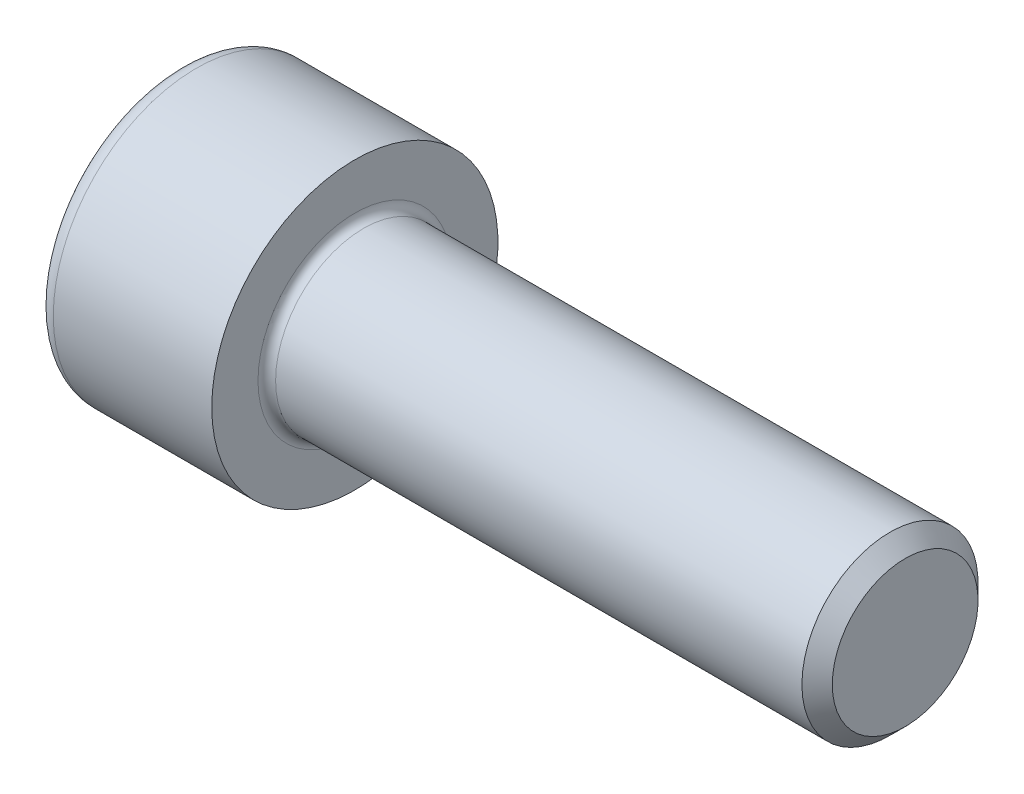
SolidWorks part; units mm, degrees
ref_plane "Plane1" through (0, 0, 0) normal (0, 0, 1) x (1, 0, 0)
ref_plane "Plane2" through (0, 0, 0) normal (0, 1, 0) x (1, 0, 0)
ref_plane "Plane3" through (0, 0, 0) normal (1, 0, 0) x (0, 0, -1)
sketch "BodySke" plane through (0, 0, 0) normal (0, 0, 1) x (1, 0, 0)
  line L0 (0, 0) -> (0, 6.5)
  line L1 (0, 6.5) -> (8, 6.5)
  line L2 (8, 6.5) -> (8, 4)
  line L3 (8, 4) -> (32.3095, 4)
  line L4 (33, 3.3095) -> (33, 0)
  line L5 (33, 0) -> (0, 0)
  line L6 (-31.75, 0) -> (127, 0) construction
  line L8 (33, 3.3095) -> (32.3095, 4)
  line L10 (33, -3.3095) -> (32.3095, -4) construction
  line L11 (9.25, 9.525) -> (9.25, 3.175) construction
  line L12 (8, 9.525) -> (8, 3.175) construction
  line L13 (-27, 9.525) -> (-27, 3.175) construction
  dimension "Diameter" = 8
  dimension "Head_ht" = 8
  dimension "Length" = 25
  dimension "Body_ch_ang" = 45
  dimension "Head_dia" = 13
  dimension "Minor_dia" = 6.619
  dimension "Advance" = 1.25
  dimension "Thread_nom" = 25
  dimension "Thread_length" = 60
revolve "Base-Revolve" add sketch "BodySke"
cosmetic thread "ThreadCosmetic" [suppressed]
fillet "Fillet1" radius 0.4 1 edges at (8, 0, 4)
fillet "Fillet2" radius 0.8 1 edges at (0, 0, 6.5)
sketch "Sketch2" plane through (0, 0, 0) normal (0, 0, 1) x (1, 0, 0)
  line L0 (0, 3.01) -> (4, 3.01)
  line L1 (4, 3.01) -> (5.7378, 0)
  line L2 (-31.75, 0) -> (127, 0) construction
  line L3 (5.7378, 0) -> (0, 0)
  line L4 (0, 0) -> (0, 3.01)
  line L6 (0, 0) -> (47.625, 0) construction
  dimension "D1" = 3.01
  dimension "D2" = 60
  dimension "Depth" = 4
revolve "Hex-PreBroach" cut sketch "Sketch2" angle 360 about L6
sketch "Sketch3" plane through (0, 0, 0) normal (-1, 0, 0) x (0, 0.5, 0.866)
  line L0 (1.7378, 3.01) -> (-1.7378, 3.01)
  line L1 (-1.7378, 3.01) -> (-3.4756, 0)
  line L2 (1.7378, 3.01) -> (3.4756, 0)
  line L3 (1.7378, -3.01) -> (3.4756, 0)
  line L4 (1.7378, -3.01) -> (-1.7378, -3.01)
  line L5 (-1.7378, -3.01) -> (-3.4756, 0)
  dimension "D1" = 3.01
  dimension "D2" = 3.01
  dimension "Hex_size" = 6.02
extrude "Hex" cut sketch "Sketch3" against normal blind 4
sketch "ThdSchSke" plane through (0, 0, 0) normal (0, 0, 1) x (1, 0, 0)
  line L0 (11.75, -3.3095) -> (11.2665, -4)
  line L1 (11.75, -3.3095) -> (12.2335, -4)
  line L2 (12.2335, -4) -> (12.2335, -5)
  line L3 (-3.175, 0) -> (5.1513, 0) construction
  line L4 (0, 5.7) -> (0, -5.7) construction
  line L5 (12.2335, -5) -> (11.2665, -5)
  line L6 (11.2665, -5) -> (11.2665, -4)
  dimension "Thread_minor" = 6.619
  dimension "Diameter" = 8
  dimension "Start" = 11.75
  dimension "SideAngle" = 55
  dimension "VeeAngle" = 70
  dimension "Overcut" = 10
revolve "ThreadSchematic" [suppressed] cut sketch "ThdSchSke" angle 360 about L3
pattern_linear "ThdSchPat" [suppressed]
equation "\"D2@Sketch3\" = \"Hex_size@Sketch3\" / 2"
equation "\"D1@Sketch3\" = \"Hex_size@Sketch3\" / 2"
equation "\"D1@Sketch2\" = \"Hex_size@Sketch3\" / 2"
equation "\"Thread_minor@ThreadCosmetic\"  =  \"Minor_dia@BodySke\""
equation "\"Depth@Sketch2\" =  \"Key_eng@Hex\""
equation "\"Thread_length@ThreadCosmetic\" = ((sgn( (\"Length@BodySke\" - \"Advance@BodySke\" * 3.0) - \"Thread_nom@BodySke\" )-1)*( (\"Length@BodySke\" - \"Advance@BodySke\" * 3.0) - \"Thread_nom@BodySke\" ))/-2+ \"Thread_nom@BodySke\""
equation "\"Thread_minor@ThdSchSke\" = \"Minor_dia@BodySke\""
equation "\"Diameter@ThdSchSke\" = \"Diameter@BodySke\""
equation "\"Overcut@ThdSchSke\" = \"Diameter@BodySke\" * 1.25"
equation "\"Start@ThdSchSke\" = \"Head_ht@BodySke\" + \"Length@BodySke\" - \"Thread_length@ThreadCosmetic\"  '---Non-countersunk---"
equation "\"Num_threads@ThdSchPat\" = int( \"Thread_length@ThreadCosmetic\" / \"Advance@BodySke\" + 0.999 )  + 1"
equation "\"Advance@ThdSchPat\" = \"Thread_length@ThreadCosmetic\" /  (\"Num_threads@ThdSchPat\" - 1) 'relax it"
equation "\"Num_threads@ThdSchPat\" = \"Num_threads@ThdSchPat\" - sgn( \"Num_threads@ThdSchPat\" - 1) '---chamfered tips only---"
